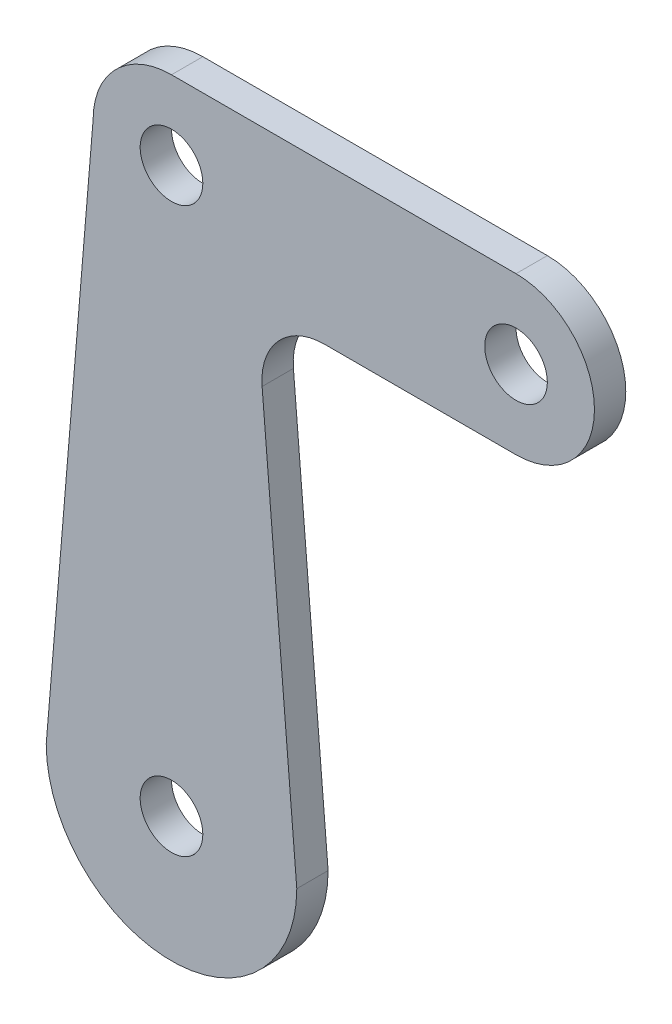
SolidWorks part; units mm, degrees
ref_plane "Front Plane" through (0, 0, 0) normal (0, 0, 1) x (1, 0, 0)
ref_plane "Top Plane" through (0, 0, 0) normal (0, 1, 0) x (1, 0, 0)
ref_plane "Right Plane" through (0, 0, 0) normal (1, 0, 0) x (0, 0, -1)
sketch "Sketch1" plane through (0, 0, 0) normal (0, 0, 1) x (1, 0, 0)
  line L0 (34.925, 7.9502) -> (34.925, -7.9502) construction
  line L1 (0, 7.9502) -> (0, -3.175) construction
  line L2 (7.9502, 0) -> (-7.9502, 0) construction
  line L3 (-12.7, -57.15) -> (12.7, -57.15) construction
  line L4 (-7.9502, 0) -> (-12.7, -57.15)
  line L5 (9.1839, -14.8259) -> (12.7, -57.15)
  line L6 (15.5121, -7.9502) -> (34.925, -7.9502)
  line L7 (34.925, 7.9502) -> (0, 7.9502)
  line L8 (0, -57.15) -> (0, 0) construction
  circle A0 centre (0, 0) radius 3.175
  circle A1 centre (34.925, 0) radius 3.175
  circle A2 centre (0, -57.15) radius 3.175
  arc A3 (34.925, -7.9502) -> (34.925, 7.9502) centre (34.925, 0) ccw
  arc A4 (-12.5258, -55.0535) -> (12.5259, -55.0543) centre (0, -57.15) ccw
  arc A5 (0, 7.9502) -> (-7.9502, 0) centre (0, 0) ccw
  arc A6 (9.1839, -14.8259) -> (15.5121, -7.9502) centre (15.5121, -14.3002) cw
  dimension "D1" = 6.35
  dimension "D4" = 15.9004
  dimension "D5" = 25.4
  dimension "D6" = 6.35
  dimension "D2" = 34.925
  dimension "D3" = 57.15
  dimension "D7" = 9.5
extrude "Boss-Extrude1" add sketch "Sketch1" along normal blind 3.175 contours L5 A6 L6 A3 L7 A5 L4 A4 A0 A1 A2
